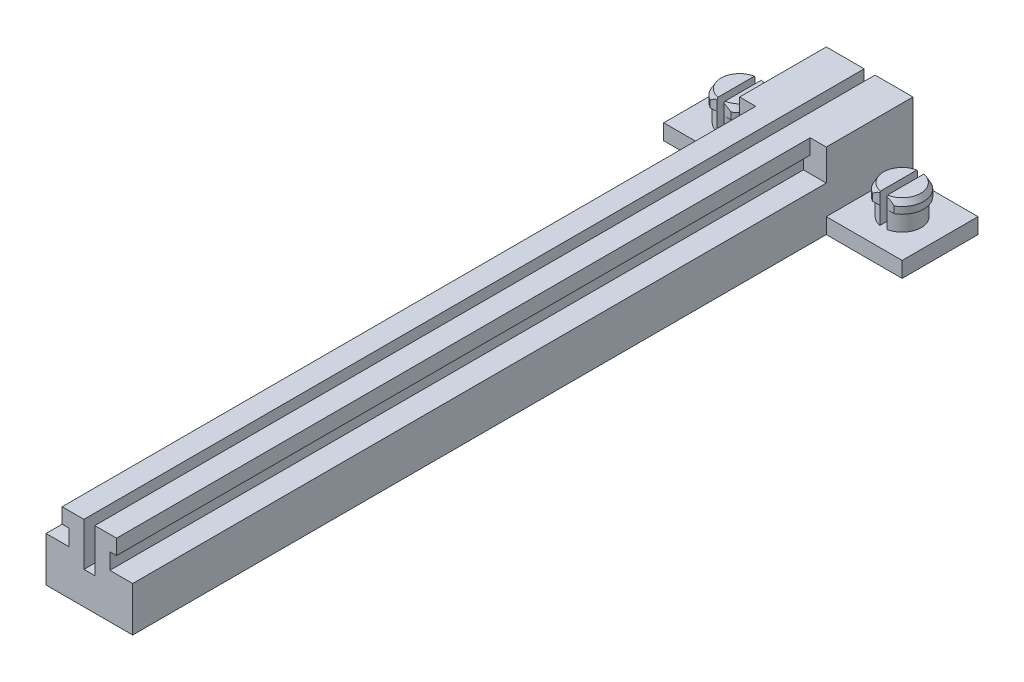
SolidWorks part; units mm, degrees
ref_plane "Front Plane" through (0, 0, 0) normal (0, 0, 1) x (1, 0, 0)
ref_plane "Top Plane" through (0, 0, 0) normal (0, 1, 0) x (1, 0, 0)
ref_plane "Right Plane" through (0, 0, 0) normal (1, 0, 0) x (0, 0, -1)
sketch "Sketch1" plane through (0, 0, 0) normal (0, 1, 0) x (1, 0, 0)
  line L1 (0, 0) -> (12.7, 0)
  line L2 (0, 0) -> (0, -114.3)
  line L3 (0, -114.3) -> (12.7, -114.3)
  line L4 (12.7, 0) -> (12.7, -114.3)
  dimension "D1" = 12.7
  dimension "D2" = 114.3
extrude "Boss-Extrude1" add sketch "Sketch1" along normal blind 11.1125
sketch "Sketch2" plane through (0, 0, 114.3) normal (0, 0, 1) x (1, 0, 0)
  line L0 (6.35, 11.1125) -> (6.35, 0) construction
  line L1 (0, 11.1125) -> (12.7, 11.1125) construction
  line L2 (0, 0) -> (12.7, 0) construction
  line L3 (0, 5.5562) -> (12.7, 5.5562) construction
  line L4 (0, 11.1125) -> (0, 0) construction
  line L5 (12.7, 11.1125) -> (12.7, 0) construction
  line L7 (5.5563, 11.1125) -> (7.1438, 11.1125)
  line L8 (5.5563, 11.1125) -> (5.5563, 4.7625)
  line L9 (5.5563, 4.7625) -> (7.1438, 4.7625)
  line L10 (7.1438, 11.1125) -> (7.1438, 4.7625)
  dimension "D1" = 1.5875
  dimension "D2" = 6.35
extrude "Cut-Extrude1" cut sketch "Sketch2" against normal through all
sketch "Sketch3" plane through (0, 0, 114.3) normal (0, 0, 1) x (1, 0, 0)
  line L0 (2.3622, 11.1125) -> (2.3622, 8.9027)
  line L2 (2.3622, 8.9027) -> (3.3465, 8.9027)
  line L3 (3.3465, 8.9027) -> (3.3465, 6.5405)
  line L4 (3.3465, 6.5405) -> (0, 6.5405)
  line L5 (0, 11.1125) -> (0, 0) construction
  line L6 (0, 6.5405) -> (0, 11.1125)
  line L7 (0, 11.1125) -> (2.3622, 11.1125)
  line L8 (10.3378, 11.1125) -> (10.3378, 8.9027)
  line L10 (10.3378, 8.9027) -> (9.3536, 8.9027)
  line L11 (9.3536, 8.9027) -> (9.3536, 6.5405)
  line L12 (9.3536, 6.5405) -> (12.7, 6.5405)
  line L13 (12.7, 11.1125) -> (12.7, 0) construction
  line L14 (12.7, 6.5405) -> (12.7, 11.1125)
  line L15 (12.7, 11.1125) -> (10.3378, 11.1125)
  line L16 (5.5563, 11.1125) -> (5.5563, 4.7625) construction
  dimension "D1" = 2.2098
  dimension "D2" = 2.2098
  dimension "D3" = 2.3622
  dimension "D4" = 2.3622
extrude "Cut-Extrude2" cut sketch "Sketch3" against normal blind 101.6
sketch "Sketch4" plane through (0, 0, 0) normal (0, -1, 0) x (1, 0, 0)
  line L0 (0, 0) -> (0, 114.3) construction
  line L1 (0, 1.5875) -> (-11.1125, 1.5875)
  line L2 (0, 1.5875) -> (0, 12.7)
  line L3 (0, 12.7) -> (-11.1125, 12.7)
  line L4 (-11.1125, 1.5875) -> (-11.1125, 12.7)
  line L5 (12.7, 1.5875) -> (23.8125, 1.5875)
  line L6 (12.7, 1.5875) -> (12.7, 12.7)
  line L7 (12.7, 12.7) -> (23.8125, 12.7)
  line L8 (23.8125, 1.5875) -> (23.8125, 12.7)
  dimension "D1" = 11.1125
  dimension "D2" = 11.1125
extrude "Boss-Extrude2" add sketch "Sketch4" against normal blind 2.286
sketch "Sketch5" plane through (0, 2.286, 0) normal (0, 1, 0) x (1, 0, 0)
  line L0 (-5.5562, -1.5875) -> (-5.5562, -12.7) construction
  line L1 (-11.1125, -1.5875) -> (0, -1.5875) construction
  line L2 (0, -12.7) -> (-11.1125, -12.7) construction
  line L3 (-11.1125, -7.1438) -> (0, -7.1438) construction
  line L4 (-11.1125, -12.7) -> (-11.1125, -1.5875) construction
  line L5 (0, -1.5875) -> (0, -12.7) construction
  line L6 (18.2563, -1.5875) -> (18.2563, -12.7) construction
  line L7 (12.7, -1.5875) -> (23.8125, -1.5875) construction
  line L8 (23.8125, -12.7) -> (12.7, -12.7) construction
  line L9 (23.8125, -7.1438) -> (12.7, -7.1438) construction
  line L10 (23.8125, -1.5875) -> (23.8125, -12.7) construction
  line L11 (12.7, -12.7) -> (12.7, -1.5875) construction
  line L12 (-5.5562, -4.3498) -> (-5.5562, -9.9378) construction
  line L13 (18.7643, -4.3963) -> (18.7643, -9.8912)
  line L14 (-6.0642, -4.3498) -> (-6.0642, -9.9378)
  line L15 (17.7483, -4.3963) -> (17.7483, -9.8912)
  line L16 (-5.0482, -4.3498) -> (-5.0482, -9.9378)
  arc A0 (-6.0642, -4.3498) -> (-6.0642, -9.9378) centre (-5.5562, -7.1438) ccw
  arc A1 (17.7483, -4.3963) -> (17.7483, -9.8912) centre (18.2563, -7.1438) ccw
  arc A2 (-5.0482, -9.9378) -> (-5.0482, -4.3498) centre (-5.5562, -7.1438) ccw
  arc A3 (18.7643, -9.8912) -> (18.7643, -4.3963) centre (18.2563, -7.1438) ccw
  dimension "D1" = 5.588
  dimension "D4" = 2.794
  dimension "D2" = 1.016
  dimension "D3" = 1.016
extrude "Boss-Extrude3" add sketch "Sketch5" along normal blind 2.54
sketch "Sketch6" plane through (0, 4.826, 0) normal (0, 1, 0) x (1, 0, 0)
  line L0 (-7.0643, -4.3498) -> (-6.0642, -4.3498)
  line L1 (-6.0642, -4.3498) -> (-6.0642, -9.9378)
  line L2 (-6.0642, -9.9378) -> (-7.0643, -9.9378)
  line L3 (-4.0482, -4.3498) -> (-5.0482, -4.3498)
  line L4 (-5.0482, -4.3498) -> (-5.0482, -9.9378)
  line L5 (-5.0482, -9.9378) -> (-4.0482, -9.9378)
  line L6 (16.6649, -4.3963) -> (17.7483, -4.3963)
  line L7 (17.7483, -4.3963) -> (17.7483, -9.8912)
  line L9 (19.8476, -4.3963) -> (18.7643, -4.3963)
  line L10 (18.7643, -4.3963) -> (18.7643, -9.8912)
  line L11 (18.7643, -9.8912) -> (19.8476, -9.8912)
  line L15 (16.6649, -9.8912) -> (17.7483, -9.8912)
  arc A0 (-7.0643, -4.3498) -> (-7.0643, -9.9378) centre (-5.5562, -7.1438) ccw
  arc A1 (16.6649, -4.3963) -> (16.6649, -9.8912) centre (18.2563, -7.1438) ccw
  arc A2 (-6.0642, -4.3498) -> (-6.0642, -9.9378) centre (-5.5562, -7.1438) ccw construction
  arc A3 (17.7483, -4.3963) -> (17.7483, -9.8912) centre (18.2563, -7.1438) ccw construction
  arc A4 (-4.0482, -9.9378) -> (-4.0482, -4.3498) centre (-5.5562, -7.1438) ccw
  arc A5 (17.7483, -4.3963) -> (17.7483, -9.8912) centre (18.2563, -7.1438) ccw construction
  arc A6 (19.8476, -9.8912) -> (19.8476, -4.3963) centre (18.2563, -7.1438) ccw
  dimension "D1" = 6.35
extrude "Boss-Extrude5" add sketch "Sketch6" along normal blind 1.778
chamfer "Chamfer1" distance 0.7937 angle 30 4 edges at (21.4313, 6.604, 7.1438) (15.0813, 6.604, 7.1438) (-2.3812, 6.604, 7.1438) (-8.7312, 6.604, 7.1438)
sketch "Sketch7" plane through (0, 0, 0) normal (0, -1, 0) x (1, 0, 0)
  line L1 (6.35, 114.3) -> (6.35, 101.6) construction
  line L2 (0, 114.3) -> (12.7, 114.3) construction
  circle A0 centre (6.35, 101.6) radius 3.302
  circle A1 centre (6.35, 44.0141) radius 3.302
  dimension "D2" = 6.604
  dimension "D1" = 57.5859
  dimension "D3" = 12.7
extrude "Cut-Extrude3" cut sketch "Sketch7" against normal blind 2.032
sketch "Sketch8" plane through (0, 2.032, 0) normal (0, -1, 0) x (1, 0, 0)
  circle A0 centre (6.35, 101.6) radius 3.556
  circle A1 centre (6.35, 44.0141) radius 3.556
  dimension "D1" = 7.112
extrude "Cut-Extrude4" cut sketch "Sketch8" against normal blind 1.905
